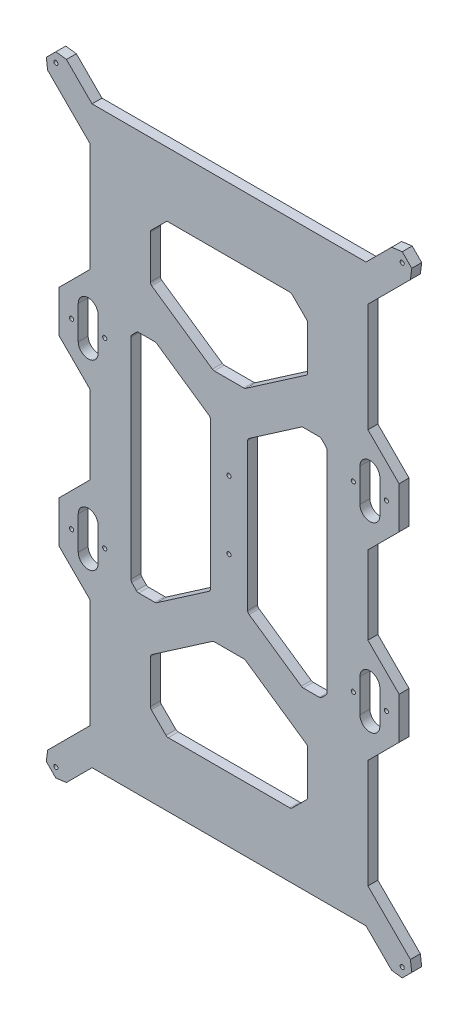
SolidWorks part; units mm, degrees
ref_plane "Piano frontale" through (0, 0, 0) normal (0, 0, 1) x (1, 0, 0)
ref_plane "Piano superiore" through (0, 0, 0) normal (0, 1, 0) x (1, 0, 0)
ref_plane "Piano destro" through (0, 0, 0) normal (1, 0, 0) x (0, 0, -1)
sketch "Schizzo1" plane through (0, 0, 0) normal (0, 0, 1) x (1, 0, 0)
  line L0 (-59.2321, 63.2717) -> (-59.2321, -63.2717)
  line L1 (79, 45) -> (79, 65)
  line L2 (-110.2802, 184.0111) -> (-104.5111, 189.7802)
  line L3 (-85, 44.8144) -> (-85, 67.8144) construction
  line L4 (-110.2802, 184.0111) -> (-109.4473, 177.6336)
  line L5 (-109.4473, 177.6336) -> (-83.8188, 152.0051)
  line L6 (-83.8188, 152.0051) -> (-83.8188, 86.4006)
  line L7 (-83.8188, 86.4006) -> (-102.629, 67.5904)
  line L8 (-83.8188, 23.5994) -> (-83.8188, -23.5994)
  line L9 (-11.2416, 44.3644) -> (-11.2416, -44.3644)
  line L10 (-79.5, 0) -> (161.9096, 0) construction
  line L11 (-47.483, 123.9389) -> (-47.483, 97.9796)
  line L12 (-46.8972, 125.3531) -> (-38.0688, 134.1815)
  line L13 (91, 45) -> (91, 65)
  line L14 (-75, 55) -> (-95, 55) construction
  line L15 (-79, 45) -> (-79, 65)
  line L16 (-104.2758, 183.7758) -> (0.2242, 79.2758) construction
  line L17 (-104.5111, 189.7802) -> (-98.1336, 188.9473)
  line L18 (-104.5, 184) -> (-161.9096, 184) construction
  line L19 (79.5, 0) -> (-161.9096, 0) construction
  line L20 (-104.5, 0) -> (-161.9096, 0) construction
  line L21 (91, -45) -> (91, -65)
  line L22 (0, 0) -> (0, 265.525) construction
  line L23 (89.75, 169.25) -> (-14.75, 64.75) construction
  line L24 (-102.629, 67.5904) -> (-102.629, 42.4096)
  line L25 (-83.8188, 23.5994) -> (-102.629, 42.4096)
  line L26 (75, 55) -> (95, 55) construction
  line L27 (79, -45) -> (79, -65)
  line L28 (-79, -45) -> (-79, -65)
  line L29 (-46.6177, 96.3326) -> (-10.0462, 71.1381)
  line L30 (-8.9116, 70.7851) -> (8.9116, 70.7851)
  line L31 (-91, -45) -> (-91, -65)
  line L33 (-82.6539, 173.4676) -> (82.6539, 173.4676)
  line L34 (98.1336, 188.9473) -> (82.6539, 173.4676)
  line L35 (43.6395, 67.7345) -> (12.1069, 46.0114)
  line L36 (54.5057, 68.0875) -> (44.7741, 68.0875)
  line L37 (58.669, 64.6629) -> (55.9425, 67.4787)
  line L38 (-58.669, 64.6629) -> (-55.9425, 67.4787)
  line L39 (-54.5057, 68.0875) -> (-44.7741, 68.0875)
  line L40 (-43.6395, 67.7345) -> (-12.1069, 46.0114)
  line L41 (46.6177, 96.3326) -> (10.0462, 71.1381)
  line L42 (83.8188, 23.5994) -> (102.629, 42.4096)
  line L43 (102.629, 67.5904) -> (102.629, 42.4096)
  line L44 (104.5111, 189.7802) -> (98.1336, 188.9473)
  line L47 (46.8972, 125.3531) -> (38.0688, 134.1815)
  line L48 (47.483, 123.9389) -> (47.483, 97.9796)
  line L49 (11.2416, 44.3644) -> (11.2416, -44.3644)
  line L50 (83.8188, 23.5994) -> (83.8188, -23.5994)
  line L51 (83.8188, 86.4006) -> (102.629, 67.5904)
  line L52 (-36.6546, 134.7673) -> (36.6546, 134.7673)
  line L53 (83.8188, 152.0051) -> (83.8188, 86.4006)
  line L54 (109.4473, 177.6336) -> (83.8188, 152.0051)
  line L55 (110.2802, 184.0111) -> (109.4473, 177.6336)
  line L56 (110.2802, 184.0111) -> (104.5111, 189.7802)
  line L57 (59.2321, 63.2717) -> (59.2321, -63.2717)
  line L60 (75, -55) -> (95, -55) construction
  line L61 (-75, -55) -> (-95, -55) construction
  line L63 (-98.1336, 188.9473) -> (-82.6539, 173.4676)
  line L67 (-98.1336, -188.9473) -> (-82.6539, -173.4676)
  line L68 (110.2802, -184.0111) -> (104.5111, -189.7802)
  line L69 (110.2802, -184.0111) -> (109.4473, -177.6336)
  line L70 (109.4473, -177.6336) -> (83.8188, -152.0051)
  line L71 (83.8188, -152.0051) -> (83.8188, -86.4006)
  line L72 (-36.6546, -134.7673) -> (36.6546, -134.7673)
  line L73 (83.8188, -86.4006) -> (102.629, -67.5904)
  line L74 (-91, 45) -> (-91, 65)
  line L76 (47.483, -123.9389) -> (47.483, -97.9796)
  line L77 (46.8972, -125.3531) -> (38.0688, -134.1815)
  line L80 (104.5111, -189.7802) -> (98.1336, -188.9473)
  line L81 (102.629, -67.5904) -> (102.629, -42.4096)
  line L82 (83.8188, -23.5994) -> (102.629, -42.4096)
  line L83 (46.6177, -96.3326) -> (10.0462, -71.1381)
  line L84 (-43.6395, -67.7345) -> (-12.1069, -46.0114)
  line L85 (-54.5057, -68.0875) -> (-44.7741, -68.0875)
  line L86 (-58.669, -64.6629) -> (-55.9425, -67.4787)
  line L87 (58.669, -64.6629) -> (55.9425, -67.4787)
  line L88 (54.5057, -68.0875) -> (44.7741, -68.0875)
  line L89 (43.6395, -67.7345) -> (12.1069, -46.0114)
  line L90 (98.1336, -188.9473) -> (82.6539, -173.4676)
  line L91 (-82.6539, -173.4676) -> (82.6539, -173.4676)
  line L94 (-8.9116, -70.7851) -> (8.9116, -70.7851)
  line L95 (-46.6177, -96.3326) -> (-10.0462, -71.1381)
  line L96 (-83.8188, -23.5994) -> (-102.629, -42.4096)
  line L97 (-102.629, -67.5904) -> (-102.629, -42.4096)
  line L98 (-104.5111, -189.7802) -> (-98.1336, -188.9473)
  line L101 (-46.8972, -125.3531) -> (-38.0688, -134.1815)
  line L102 (-47.483, -123.9389) -> (-47.483, -97.9796)
  line L103 (-83.8188, -86.4006) -> (-102.629, -67.5904)
  line L104 (-83.8188, -152.0051) -> (-83.8188, -86.4006)
  line L105 (-109.4473, -177.6336) -> (-83.8188, -152.0051)
  line L106 (-110.2802, -184.0111) -> (-109.4473, -177.6336)
  line L107 (-110.2802, -184.0111) -> (-104.5111, -189.7802)
  circle A0 centre (-95, 55) radius 1.25
  circle A1 centre (-75, 55) radius 1.25
  arc A2 (-91, 65) -> (-79, 65) centre (-85, 65) cw
  arc A3 (-91, 45) -> (-79, 45) centre (-85, 45) ccw
  arc A4 (-44.7741, 68.0875) -> (-43.6395, 67.7345) centre (-44.7741, 66.0875) cw
  arc A5 (-54.5057, 68.0875) -> (-55.9425, 67.4787) centre (-54.5057, 66.0875) ccw
  circle A6 centre (-104.5, 184) radius 1.25
  arc A7 (-58.669, 64.6629) -> (-59.2321, 63.2717) centre (-57.2321, 63.2717) ccw
  arc A8 (-36.6546, 134.7673) -> (-38.0688, 134.1815) centre (-36.6546, 132.7673) ccw
  arc A9 (-46.8972, 125.3531) -> (-47.483, 123.9389) centre (-45.483, 123.9389) ccw
  arc A10 (-47.483, 97.9796) -> (-46.6177, 96.3326) centre (-45.483, 97.9796) ccw
  arc A11 (-10.0462, 71.1381) -> (-8.9116, 70.7851) centre (-8.9116, 72.7851) ccw
  arc A12 (11.2416, 44.3644) -> (12.1069, 46.0114) centre (13.2416, 44.3644) cw
  arc A13 (91, 45) -> (79, 45) centre (85, 45) cw
  arc A14 (91, 65) -> (79, 65) centre (85, 65) ccw
  circle A15 centre (0, 20.5) radius 1.25
  arc A16 (10.0462, 71.1381) -> (8.9116, 70.7851) centre (8.9116, 72.7851) cw
  arc A17 (91, -45) -> (79, -45) centre (85, -45) ccw
  arc A18 (47.483, 97.9796) -> (46.6177, 96.3326) centre (45.483, 97.9796) cw
  arc A19 (91, -65) -> (79, -65) centre (85, -65) cw
  arc A20 (46.8972, 125.3531) -> (47.483, 123.9389) centre (45.483, 123.9389) cw
  arc A21 (36.6546, 134.7673) -> (38.0688, 134.1815) centre (36.6546, 132.7673) cw
  arc A22 (58.669, 64.6629) -> (59.2321, 63.2717) centre (57.2321, 63.2717) cw
  circle A23 centre (104.5, 184) radius 1.25
  arc A24 (54.5057, 68.0875) -> (55.9425, 67.4787) centre (54.5057, 66.0875) cw
  arc A25 (44.7741, 68.0875) -> (43.6395, 67.7345) centre (44.7741, 66.0875) ccw
  arc A26 (-91, -45) -> (-79, -45) centre (-85, -45) cw
  arc A27 (-91, -65) -> (-79, -65) centre (-85, -65) ccw
  circle A28 centre (75, 55) radius 1.25
  circle A29 centre (95, 55) radius 1.25
  arc A30 (-11.2416, 44.3644) -> (-12.1069, 46.0114) centre (-13.2416, 44.3644) ccw
  arc A31 (-11.2416, -44.3644) -> (-12.1069, -46.0114) centre (-13.2416, -44.3644) cw
  circle A32 centre (95, -55) radius 1.25
  circle A33 centre (75, -55) radius 1.25
  arc A36 (44.7741, -68.0875) -> (43.6395, -67.7345) centre (44.7741, -66.0875) cw
  arc A37 (54.5057, -68.0875) -> (55.9425, -67.4787) centre (54.5057, -66.0875) ccw
  circle A38 centre (104.5, -184) radius 1.25
  arc A39 (58.669, -64.6629) -> (59.2321, -63.2717) centre (57.2321, -63.2717) ccw
  arc A40 (36.6546, -134.7673) -> (38.0688, -134.1815) centre (36.6546, -132.7673) ccw
  arc A41 (46.8972, -125.3531) -> (47.483, -123.9389) centre (45.483, -123.9389) ccw
  arc A43 (47.483, -97.9796) -> (46.6177, -96.3326) centre (45.483, -97.9796) ccw
  arc A45 (10.0462, -71.1381) -> (8.9116, -70.7851) centre (8.9116, -72.7851) ccw
  circle A46 centre (0, -20.5) radius 1.25
  arc A49 (11.2416, -44.3644) -> (12.1069, -46.0114) centre (13.2416, -44.3644) ccw
  arc A50 (-10.0462, -71.1381) -> (-8.9116, -70.7851) centre (-8.9116, -72.7851) cw
  arc A51 (-47.483, -97.9796) -> (-46.6177, -96.3326) centre (-45.483, -97.9796) cw
  arc A52 (-46.8972, -125.3531) -> (-47.483, -123.9389) centre (-45.483, -123.9389) cw
  arc A53 (-36.6546, -134.7673) -> (-38.0688, -134.1815) centre (-36.6546, -132.7673) cw
  arc A54 (-58.669, -64.6629) -> (-59.2321, -63.2717) centre (-57.2321, -63.2717) cw
  circle A55 centre (-104.5, -184) radius 1.25
  arc A56 (-54.5057, -68.0875) -> (-55.9425, -67.4787) centre (-54.5057, -66.0875) cw
  arc A57 (-44.7741, -68.0875) -> (-43.6395, -67.7345) centre (-44.7741, -66.0875) ccw
  circle A60 centre (-75, -55) radius 1.25
  circle A61 centre (-95, -55) radius 1.25
  point P1 (0, 70.7851)
  point P9 (-66.4357, 0)
  point P10 (-109.1466, 0)
  point P17 (-79, 55)
  point P20 (-91, 55)
  point P24 (-83.8188, 0)
  point P26 (-107.3957, 186.8957)
  point P51 (-37.483, 134.7673)
  point P55 (-47.483, 124.7673)
  point P66 (-66.4357, 0)
  point P69 (0, 134.7673)
  point P72 (-102.629, 55)
  point P77 (0, 173.4676)
  point P78 (0, 70.7851)
  point P87 (0, 173.4676)
  point P133 (-47.483, 134.7673)
  point P134 (0, 134.7673)
  point P139 (11.2416, 0)
  point P145 (66.4357, 0)
  point P146 (9.2567, 0)
  point P147 (47.483, 134.7673)
  point P148 (102.629, 55)
  point P152 (47.483, 124.7673)
  point P153 (37.483, 134.7673)
  point P154 (107.3957, 186.8957)
  point P157 (109.1466, 0)
  point P194 (-9.2567, 0)
  point P198 (-66.4357, 0)
  point P254 (59.2321, 0)
  point P261 (83.8188, 0)
  point P268 (-11.2416, 0)
  point P272 (-59.2321, 0)
  point P273 (-9.2567, 0)
  point P274 (109.1466, 0)
  point P277 (107.3957, -186.8957)
  point P278 (37.483, -134.7673)
  point P279 (47.483, -124.7673)
  point P280 (102.629, -55)
  point P281 (47.483, -134.7673)
  point P282 (9.2567, 0)
  point P283 (66.4357, 0)
  point P284 (0, -134.7673)
  point P285 (-47.483, -134.7673)
  point P286 (0, -173.4676)
  point P287 (0, -70.7851)
  point P288 (-102.629, -55)
  point P289 (-47.483, -124.7673)
  point P290 (-37.483, -134.7673)
  point P291 (-107.3957, -186.8957)
  point P294 (-109.1466, 0)
  dimension "D2" = 104.5
  dimension "D3" = 20
  dimension "D5" = 2
  dimension "D6" = 85
  dimension "D11" = 184
  dimension "D12" = 2
  dimension "D13" = 2
  dimension "D15" = 2.5
  dimension "D16" = 2.5
  dimension "D17" = 2.5
  dimension "D7" = 10
  dimension "D8" = 45
  dimension "D9" = 16
  dimension "D10" = 55
  dimension "D14" = 20.5
  dimension "D18" = 12
extrude "Estrusione-Estrusione1" add sketch "Schizzo1" against normal blind 6
sketch "Schizzo2" [suppressed] plane through (0, 0, 0) normal (0, 0, 1) x (1, 0, 0)
  line L0 (0, 0) -> (0, 148.2594) construction
  line L1 (58.9422, 84.4201) -> (-108.2298, 84.4201) construction
  line L2 (58.9422, 68.7002) -> (58.9422, 100.14) construction
  line L3 (0, 0) -> (-115.6703, 0) construction
  point P0 (29.4418, 84.4201)
  point P8 (-29.4418, 84.4201)
  point P10 (-55.8026, 0)
  point P12 (-29.4418, 0)
  point P13 (55.8026, 0)
  point P14 (29.4418, 0)
  point P15 (29.4418, -84.4201)
  point P16 (-29.4418, -84.4201)
